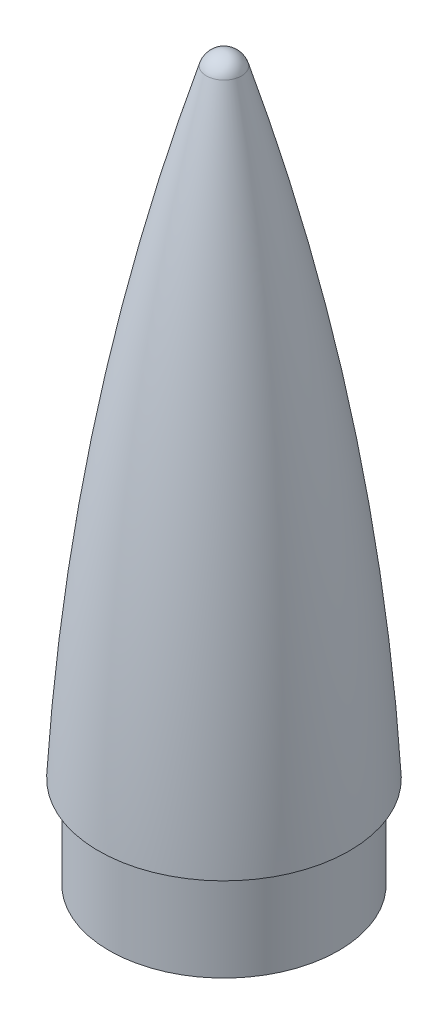
SolidWorks part; units mm, degrees
ref_plane "Front Plane" through (0, 0, 0) normal (0, 0, 1) x (1, 0, 0)
ref_plane "Top Plane" through (0, 0, 0) normal (0, 1, 0) x (1, 0, 0)
ref_plane "Right Plane" through (0, 0, 0) normal (1, 0, 0) x (0, 0, -1)
sketch "Sketch1" plane through (0, 0, 0) normal (0, 0, 1) x (1, 0, 0)
  line L0 (0, 0) -> (0, 110) construction
  line L1 (0, 0) -> (-20.5, 0) construction
  line L2 (0, -1000) -> (0, 49000) construction
  line L3 (-20.5, 0) -> (-18.75, 0)
  line L4 (-18.75, 0) -> (-18.75, -15)
  line L5 (-18.75, -15) -> (-17.25, -15)
  line L6 (-17.25, -15) -> (-17.25, -0.8416)
  line L7 (0, 103.0207) -> (0, 100.0207) construction
  line L12 (0, 103.0207) -> (0, 99.0207)
  arc A0 (-2.8712, 100.8902) -> (-20.5, 0) centre (402.9207, -22) ccw
  arc A1 (0, 103.0207) -> (-2.8712, 100.8902) centre (0, 100.0207) ccw
  arc A2 (0, 110) -> (-2.8712, 100.8902) centre (402.9207, -22) ccw construction
  arc A5 (0, 99.0207) -> (-17.25, -0.8416) centre (402.9207, -22) ccw
  point P8 (0, 0)
  point P15 (0, 0)
  point P20 (-17.25, 21.1609)
  point P21 (-17.25, 14.8814)
  point P28 (0, 0)
  point P30 (0, 0)
  dimension "D4" = 6
  dimension "D1" = 110
  dimension "D2" = 41
  dimension "D3" = 22
  dimension "D6" = 37.5
  dimension "D7" = 1.5
  dimension "D8" = 4
  dimension "D9" = 15
revolve "Revolve2" add sketch "Sketch1" angle 360 about L2
sketch "Sketch2" plane through (0, -15, 0) normal (0, -1, 0) x (1, 0, 0)
  line L0 (-9.25, 0) -> (9.25, 0) construction
  circle A0 centre (-9.25, 0) radius 9.25
  circle A1 centre (9.25, 0) radius 9.25
  dimension "D1" = 18.5
extrude "Cut-Extrude2" cut sketch "Sketch2" against normal blind 40
equation "\"Length\"=110"
equation "\"D1@Sketch1\"=\"Length\""
equation "\"Diameter\"=41"
equation "\"D2@Sketch1\"=\"Diameter\""
equation "\"D3@Sketch1\"=0.2*\"Length\""
equation "\"Shoulder\"=15"
equation "\"D9@Sketch1\"=\"Shoulder\""
